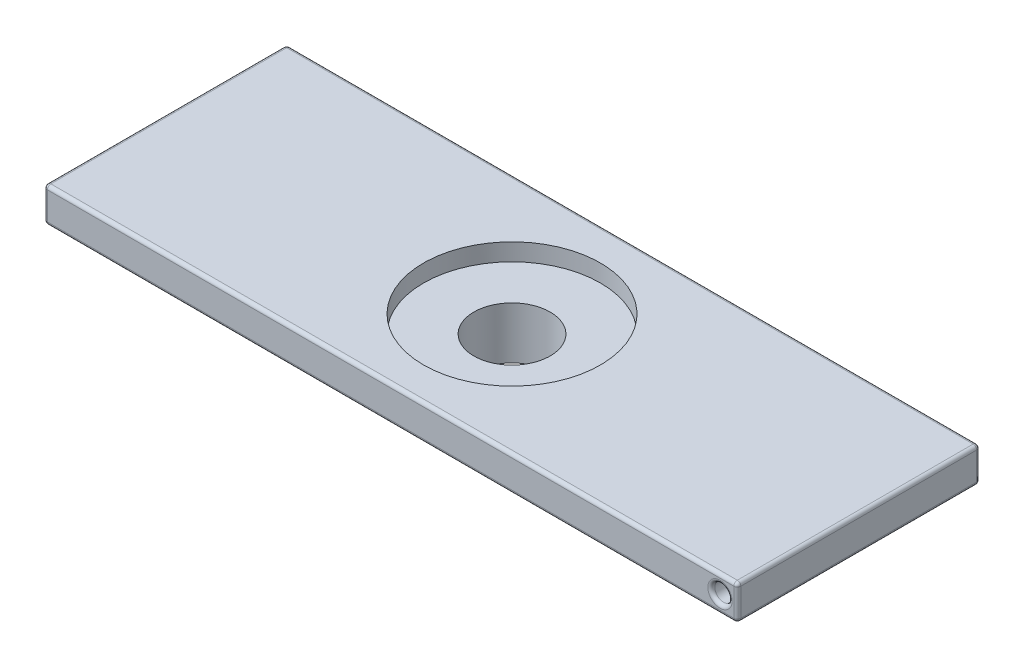
SolidWorks part; units mm, degrees
ref_plane "Front Plane" through (0, 0, 0) normal (0, 0, 1) x (1, 0, 0)
ref_plane "Top Plane" through (0, 0, 0) normal (0, 1, 0) x (1, 0, 0)
ref_plane "Right Plane" through (0, 0, 0) normal (1, 0, 0) x (0, 0, -1)
sketch "Sketch1" plane through (0, 0, 0) normal (0, 1, 0) x (1, 0, 0)
  circle A0 centre (0, 0) radius 11
  circle A1 centre (0, 0) radius 12
  dimension "D1" = 22
  dimension "D2" = 1
extrude "Boss-Extrude1" add sketch "Sketch1" along normal blind 10
sketch "Sketch2" plane through (0, 10, 0) normal (0, 1, 0) x (1, 0, 0)
  line L1 (-100, -35) -> (100, -35)
  line L2 (-100, -35) -> (-100, 35)
  line L3 (-100, 35) -> (100, 35)
  line L4 (100, -35) -> (100, 35)
  line L5 (-100, -35) -> (100, 35) construction
  line L6 (-100, 35) -> (100, -35) construction
  point P0 (0, 0)
  dimension "D1" = 200
  dimension "D2" = 70
extrude "Boss-Extrude2" add sketch "Sketch2" along normal blind 10
sketch "Sketch3" plane through (0, 10, 0) normal (0, -1, 0) x (1, 0, 0)
  circle A1 centre (0, 0) radius 11
  circle A2 centre (0, 0) radius 11
  dimension "D1" = 0
extrude "Cut-Extrude1" cut sketch "Sketch3" against normal up to next
sketch "Sketch4" plane through (0, 20, 0) normal (0, 1, 0) x (1, 0, 0)
  circle A0 centre (0, 0) radius 25.5
  dimension "D1" = 51
extrude "Cut-Extrude2" cut sketch "Sketch4" against normal offset from surface (5 mm away) 5 up to face at (0, 20, -11)
sketch "Sketch5" plane through (0, 0, 35) normal (0, 0, 1) x (1, 0, 0)
  circle A0 centre (95, 15) radius 2.5
  dimension "D1" = 5
  dimension "D2" = 95
  dimension "D3" = 15
sketch "Sketch6" plane through (0, 0, -35) normal (0, 0, -1) x (-1, 0, 0)
  circle A0 centre (95, 15) radius 2.5
  dimension "D1" = 5
  dimension "D2" = 95
  dimension "D3" = 15
extrude "Cut-Extrude3" cut sketch "Sketch5" against normal blind 40
extrude "Cut-Extrude4" cut sketch "Sketch6" against normal blind 40
fillet "Fillet1" radius 1 14 edges at (100, 20, 0) (100, 10, 0) (100, 15, -35) (0, 20, -35) (0, 10, -35) (-97.5, 15, -35) (-100, 15, -35) (-100, 20, 0) (-100, 10, 0) (-100, 15, 35) (0, 20, 35) (100, 15, 35) (0, 10, 35) (97.5, 15, 35)
